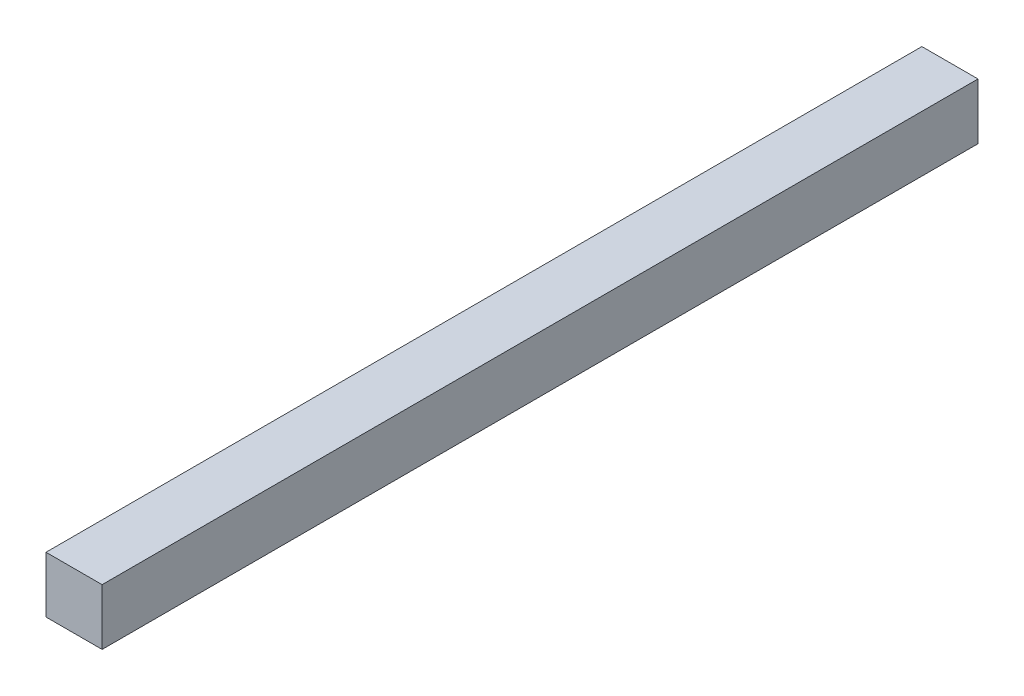
SolidWorks part; units mm, degrees
ref_plane "前视基准面" through (0, 0, 0) normal (0, 0, 1) x (1, 0, 0)
ref_plane "上视基准面" through (0, 0, 0) normal (0, 1, 0) x (1, 0, 0)
ref_plane "右视基准面" through (0, 0, 0) normal (1, 0, 0) x (0, 0, -1)
sketch "草图1" plane through (0, 0, 0) normal (0, 0, 1) x (1, 0, 0)
  line L1 (-10, -10) -> (10, -10)
  line L2 (-10, -10) -> (-10, 10)
  line L3 (-10, 10) -> (10, 10)
  line L4 (10, -10) -> (10, 10)
  line L5 (-10, -10) -> (10, 10) construction
  line L6 (-10, 10) -> (10, -10) construction
  point P0 (0, 0)
  dimension "D1" = 20
  dimension "D2" = 20
extrude "凸台-拉伸1" add sketch "草图1" along normal blind 312.2
